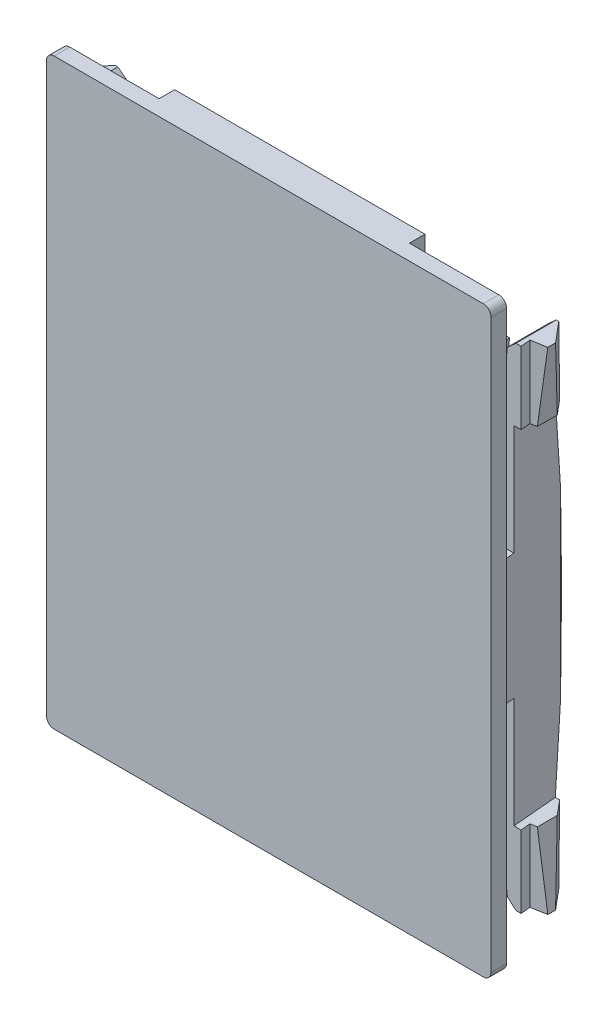
SolidWorks part; units mm, degrees
ref_plane "Front Plane" through (0, 0, 0) normal (0, 0, 1) x (1, 0, 0)
ref_plane "Top Plane" through (0, 0, 0) normal (0, 1, 0) x (1, 0, 0)
ref_plane "Right Plane" through (0, 0, 0) normal (1, 0, 0) x (0, 0, -1)
ref_plane "Plane1" through (0, 0, 0) normal (0, 0, 1) x (1, 0, 0)
sketch "Sketch1" plane through (0, 0, 0) normal (0, 0, 1) x (1, 0, 0)
  line L0 (-14.3, 18.25) -> (-14.3, -18.25)
  line L1 (-13.8, -18.75) -> (13.8, -18.75)
  line L2 (14.3, -18.25) -> (14.3, 18.25)
  line L3 (13.8, 18.75) -> (-13.8, 18.75)
  arc A0 (-14.3, -18.25) -> (-13.8, -18.75) centre (-13.8, -18.25) ccw
  arc A1 (13.8, -18.75) -> (14.3, -18.25) centre (13.8, -18.25) ccw
  arc A2 (14.3, 18.25) -> (13.8, 18.75) centre (13.8, 18.25) ccw
  arc A3 (-13.8, 18.75) -> (-14.3, 18.25) centre (-13.8, 18.25) ccw
extrude "Boss-Extrude1" add sketch "Sketch1" along normal blind 2
ref_plane "Plane2" through (0, 0, 0) normal (0, 0, 1) x (1, 0, 0)
sketch "Sketch2" plane through (0, 0, 0) normal (0, 0, 1) x (1, 0, 0)
  line L0 (-13.1, 12.5) -> (-10.1, 12.5)
  line L1 (-10.1, 14) -> (-13.1, 14)
  line L2 (-13.1, 14) -> (-13.1, 12.5)
  arc A0 (-10.1, 12.5) -> (-10.1, 14) centre (-10.1, 13.25) ccw
extrude "Boss-Extrude2" add sketch "Sketch2" against normal blind 1.7 and the other way blind 1.7
ref_plane "Plane3" through (0, 0, 0) normal (0, 0, 1) x (1, 0, 0)
sketch "Sketch3" plane through (0, 0, 0) normal (0, 0, 1) x (1, 0, 0)
  line L0 (10.1, -14) -> (13.1, -14)
  line L1 (13.1, -14) -> (13.1, -12.5)
  line L2 (13.1, -12.5) -> (10.1, -12.5)
  arc A0 (10.1, -12.5) -> (10.1, -14) centre (10.1, -13.25) ccw
extrude "Boss-Extrude3" add sketch "Sketch3" against normal blind 1.7 and the other way blind 1.7
ref_plane "Plane4" through (0, 0, 0) normal (0, 0, 1) x (1, 0, 0)
sketch "Sketch4" plane through (0, 0, 0) normal (0, 0, 1) x (1, 0, 0)
  line L0 (-13.1, -12.5) -> (-13.1, -14)
  line L1 (-13.1, -14) -> (-10.1, -14)
  line L2 (-10.1, -12.5) -> (-13.1, -12.5)
  arc A0 (-10.1, -14) -> (-10.1, -12.5) centre (-10.1, -13.25) ccw
extrude "Boss-Extrude4" add sketch "Sketch4" against normal blind 1.7 and the other way blind 1.7
ref_plane "Plane5" through (0, 0, 0) normal (0, 0, 1) x (1, 0, 0)
sketch "Sketch5" plane through (0, 0, 0) normal (0, 0, 1) x (1, 0, 0)
  line L0 (10.1, 12.5) -> (13.1, 12.5)
  line L1 (13.1, 12.5) -> (13.1, 14)
  line L2 (13.1, 14) -> (10.1, 14)
  arc A0 (10.1, 14) -> (10.1, 12.5) centre (10.1, 13.25) ccw
extrude "Boss-Extrude5" add sketch "Sketch5" against normal blind 1.7 and the other way blind 1.7
ref_plane "Plane6" through (0, 0, -3) normal (0, 0, 1) x (1, 0, 0)
sketch "Sketch6" plane through (0, 0, -3) normal (0, 0, 1) x (1, 0, 0)
  line L0 (-19.3, 23.75) -> (-19.3, -23.75)
  line L1 (-19.3, -23.75) -> (19.3, -23.75)
  line L2 (19.3, -23.75) -> (19.3, 23.75)
  line L3 (19.3, 23.75) -> (-19.3, 23.75)
  line L4 (-14.3, -4.045) -> (-11.299, -4.045)
  line L5 (-10.8017, -4.5973) -> (-11.79, -14)
  line L6 (-11.79, -14) -> (-8.55, -14)
  line L7 (-8.05, -14.5) -> (-8.05, -18.75)
  line L8 (-8.05, -18.75) -> (8.05, -18.75)
  line L9 (8.05, -18.75) -> (8.05, -14.5)
  line L10 (8.55, -14) -> (11.79, -14)
  line L11 (11.79, -14) -> (10.8017, -4.5973)
  line L12 (11.299, -4.045) -> (14.3, -4.045)
  line L13 (14.3, -4.045) -> (14.3, 4.045)
  line L14 (14.3, 4.045) -> (11.299, 4.045)
  line L15 (10.8017, 4.5973) -> (11.79, 14)
  line L16 (11.79, 14) -> (8.55, 14)
  line L17 (8.05, 14.5) -> (8.05, 18.75)
  line L18 (8.05, 18.75) -> (-8.05, 18.75)
  line L19 (-8.05, 18.75) -> (-8.05, 14.5)
  line L20 (-8.55, 14) -> (-11.79, 14)
  line L21 (-11.79, 14) -> (-10.8017, 4.5973)
  line L22 (-11.299, 4.045) -> (-14.3, 4.045)
  line L23 (-14.3, 4.045) -> (-14.3, -4.045)
  arc A0 (-11.299, -4.045) -> (-10.8017, -4.5973) centre (-11.299, -4.545) cw
  arc A1 (-8.55, -14) -> (-8.05, -14.5) centre (-8.55, -14.5) cw
  arc A2 (8.05, -14.5) -> (8.55, -14) centre (8.55, -14.5) cw
  arc A3 (10.8017, -4.5973) -> (11.299, -4.045) centre (11.299, -4.545) cw
  arc A4 (11.299, 4.045) -> (10.8017, 4.5973) centre (11.299, 4.545) cw
  arc A5 (8.55, 14) -> (8.05, 14.5) centre (8.55, 14.5) cw
  arc A6 (-8.05, 14.5) -> (-8.55, 14) centre (-8.55, 14.5) cw
  arc A7 (-10.8017, 4.5973) -> (-11.299, 4.045) centre (-11.299, 4.545) cw
extrude "Cut-Extrude1" cut sketch "Sketch6" along normal blind 4
ref_plane "Plane7" through (0, 0, -3.6) normal (0, 0, 1) x (1, 0, 0)
sketch "Sketch7" plane through (0, 0, -3.6) normal (0, 0, 1) x (1, 0, 0)
  line L0 (12.36, -4.0022) -> (13.5477, -15.3027)
  line L1 (13.5477, -15.3027) -> (14.1, -15.8)
  line L2 (14.1, -15.8) -> (15.35, -15.8)
  line L3 (15.35, -15.8) -> (14.7791, -11.15)
  line L4 (14.7791, -11.15) -> (14.04, -11.15)
  line L5 (14.04, -11.15) -> (14.04, 11.15)
  line L6 (14.04, 11.15) -> (14.7791, 11.15)
  line L7 (14.7791, 11.15) -> (15.35, 15.8)
  line L8 (15.35, 15.8) -> (14.1, 15.8)
  line L9 (14.1, 15.8) -> (13.5477, 15.3027)
  line L10 (13.5477, 15.3027) -> (12.36, 4.0022)
  line L11 (12.36, 4.0022) -> (12.36, -4.0022)
extrude "Boss-Extrude6" add sketch "Sketch7" along normal blind 3.8
ref_plane "Plane8" through (0, 0, -3.6) normal (0, 0, 1) x (1, 0, 0)
sketch "Sketch8" plane through (0, 0, -3.6) normal (0, 0, 1) x (1, 0, 0)
  line L0 (-15.35, -15.8) -> (-14.1, -15.8)
  line L1 (-14.1, -15.8) -> (-13.5477, -15.3027)
  line L2 (-13.5477, -15.3027) -> (-12.36, -4.0022)
  line L3 (-12.36, -4.0022) -> (-12.36, 4.0022)
  line L4 (-12.36, 4.0022) -> (-13.5477, 15.3027)
  line L5 (-13.5477, 15.3027) -> (-14.1, 15.8)
  line L6 (-14.1, 15.8) -> (-15.35, 15.8)
  line L7 (-15.35, 15.8) -> (-14.7791, 11.15)
  line L8 (-14.7791, 11.15) -> (-14.04, 11.15)
  line L9 (-14.04, 11.15) -> (-14.04, -11.15)
  line L10 (-14.04, -11.15) -> (-14.7791, -11.15)
  line L11 (-14.7791, -11.15) -> (-15.35, -15.8)
extrude "Boss-Extrude7" add sketch "Sketch8" along normal blind 3.8
ref_plane "Plane9" through (0, 0, 0) normal (1, 0, 0) x (0, 0, -1)
sketch "Sketch9" plane through (0, 0, 0) normal (1, 0, 0) x (0, 0, -1)
  line L0 (2.3952, -15.8) -> (8.5, -15.8)
  line L1 (8.5, -15.8) -> (8.5, 15.8)
  line L2 (8.5, 15.8) -> (2.3952, 15.8)
  line L3 (2.3952, 15.8) -> (3.5, 0)
  line L4 (3.5, 0) -> (2.3952, -15.8)
extrude "Cut-Extrude2" cut sketch "Sketch9" against normal blind 20 and the other way blind 20
ref_plane "Plane10" through (0, 0, 0) normal (0, 1, 0) x (1, 0, 0)
sketch "Sketch10" plane through (0, 0, 0) normal (0, 1, 0) x (1, 0, 0)
  line L0 (13.6026, 4) -> (14.04, -1)
  line L1 (14.04, -1) -> (14.3, -1)
  line L2 (14.3, -1) -> (14.3, 4)
  line L3 (14.3, 4) -> (13.6026, 4)
extrude "Cut-Extrude3" cut sketch "Sketch10" against normal blind 11.15 and the other way blind 11.15
ref_plane "Plane11" through (0, 0, 0) normal (0, 1, 0) x (1, 0, 0)
sketch "Sketch11" plane through (0, 0, 0) normal (0, 1, 0) x (1, 0, 0)
  line L0 (-14.3, 4) -> (-14.3, -1)
  line L1 (-14.3, -1) -> (-14.04, -1)
  line L2 (-14.04, -1) -> (-13.6026, 4)
  line L3 (-13.6026, 4) -> (-14.3, 4)
extrude "Cut-Extrude4" cut sketch "Sketch11" against normal blind 11.15 and the other way blind 11.15
ref_plane "Plane12" through (0, 0, 0) normal (0, 1, 0) x (1, 0, 0)
sketch "Sketch12" plane through (0, 0, 0) normal (0, 1, 0) x (1, 0, 0)
  line L0 (12.35, 4.8) -> (12.35, 4.6753)
  line L1 (12.35, 4.6753) -> (15.35, 1.1)
  line L2 (15.35, 1.1) -> (15.35, 0.6)
  line L3 (15.35, 0.6) -> (14.375, 0.4281)
  line L4 (14.375, 0.4281) -> (14.43, -0.2)
  line L5 (14.43, -0.2) -> (17.35, -0.2)
  line L6 (17.35, -0.2) -> (17.35, 4.8)
  line L7 (17.35, 4.8) -> (12.35, 4.8)
extrude "Cut-Extrude5" cut sketch "Sketch12" against normal blind 16 and the other way blind 16
ref_plane "Plane13" through (0, 0, 0) normal (0, 1, 0) x (1, 0, 0)
sketch "Sketch13" plane through (0, 0, 0) normal (0, 1, 0) x (1, 0, 0)
  line L0 (-17.35, 4.8) -> (-17.35, -0.2)
  line L1 (-17.35, -0.2) -> (-14.43, -0.2)
  line L2 (-14.43, -0.2) -> (-14.375, 0.4281)
  line L3 (-14.375, 0.4281) -> (-15.35, 0.6)
  line L4 (-15.35, 0.6) -> (-15.35, 1.1)
  line L5 (-15.35, 1.1) -> (-12.35, 4.6753)
  line L6 (-12.35, 4.6753) -> (-12.35, 4.8)
  line L7 (-12.35, 4.8) -> (-17.35, 4.8)
extrude "Cut-Extrude6" cut sketch "Sketch13" against normal blind 16 and the other way blind 16
